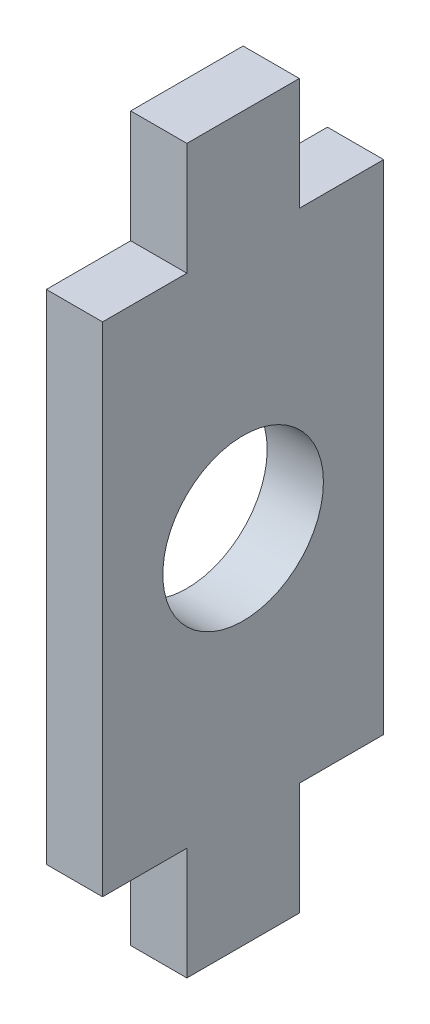
SolidWorks part; units mm, degrees
ref_plane "Front Plane" through (0, 0, 0) normal (0, 0, 1) x (1, 0, 0)
ref_plane "Top Plane" through (0, 0, 0) normal (0, 1, 0) x (1, 0, 0)
ref_plane "Right Plane" through (0, 0, 0) normal (1, 0, 0) x (0, 0, -1)
sketch "Sketch1" plane through (0, 0, 0) normal (1, 0, 0) x (0, 0, -1)
  line L1 (-17.5, -45) -> (17.5, -45)
  line L2 (-17.5, -45) -> (-17.5, 45)
  line L3 (-17.5, 45) -> (17.5, 45)
  line L4 (17.5, -45) -> (17.5, 45)
  line L5 (-17.5, -45) -> (17.5, 45) construction
  line L6 (-17.5, 45) -> (17.5, -45) construction
  line L7 (-17.5, 45) -> (-7, 45)
  line L8 (-17.5, 45) -> (-17.5, 31)
  line L9 (-17.5, 31) -> (-7, 31)
  line L10 (-7, 45) -> (-7, 31)
  line L11 (17.5, 45) -> (7, 45)
  line L12 (17.5, 45) -> (17.5, 31)
  line L13 (17.5, 31) -> (7, 31)
  line L14 (7, 45) -> (7, 31)
  line L15 (-17.5, -45) -> (-7, -45)
  line L16 (-17.5, -45) -> (-17.5, -31)
  line L17 (-17.5, -31) -> (-7, -31)
  line L18 (-7, -45) -> (-7, -31)
  line L19 (17.5, -45) -> (7, -45)
  line L20 (17.5, -45) -> (17.5, -31)
  line L21 (17.5, -31) -> (7, -31)
  line L22 (7, -45) -> (7, -31)
  point P1 (0, 0)
  dimension "D1" = 35
  dimension "D2" = 90
  dimension "D4" = 14
  dimension "D5" = 14
extrude "Boss-Extrude1" add sketch "Sketch1" along normal blind 7
sketch "Sketch2" plane through (7, 0, 0) normal (1, 0, 0) x (0, 0, -1)
  circle A0 centre (0, 0) radius 10
  dimension "D1" = 20
extrude "Cut-Extrude1" cut sketch "Sketch2" against normal through all
sketch "Sketch4" [suppressed] plane through (7, 0, 0) normal (1, 0, 0) x (0, 0, -1)
  circle A0 centre (0, 0) radius 14.2875
  dimension "D1" = 28.575
extrude "Cut-Extrude2" [suppressed] cut sketch "Sketch4" against normal through all
